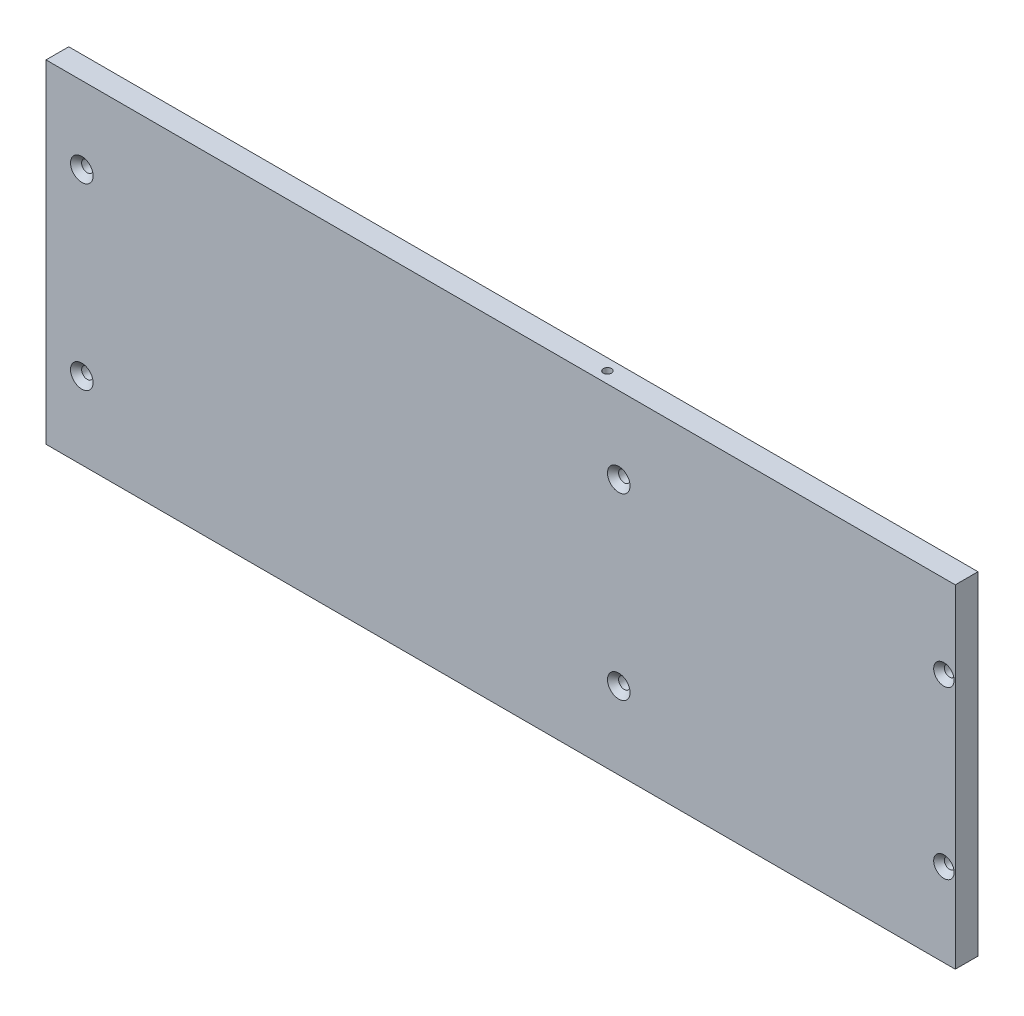
SolidWorks part; units mm, degrees
material "Perspex (TM) GS Acrylic Cast Sheet"
ref_plane "Front Plane" through (0, 0, 0) normal (0, 0, 1) x (1, 0, 0)
ref_plane "Top Plane" through (0, 0, 0) normal (0, 1, 0) x (1, 0, 0)
ref_plane "Right Plane" through (0, 0, 0) normal (1, 0, 0) x (0, 0, -1)
other "Configuration Table"
sketch "Sketch1" plane through (0, 0, 0) normal (0, 0, 1) x (1, 0, 0)
  line L1 (-127, 46.5) -> (127, 46.5)
  line L2 (-127, 46.5) -> (-127, -46.5)
  line L3 (-127, -46.5) -> (127, -46.5)
  line L4 (127, 46.5) -> (127, -46.5)
  line L5 (-127, 46.5) -> (127, -46.5) construction
  line L6 (-127, -46.5) -> (127, 46.5) construction
  point P0 (0, 0)
  dimension "D1" = 93
  dimension "D2" = 254
extrude "Boss-Extrude1" add sketch "Sketch1" along normal blind 6.35
sketch "PSU Holes" plane through (0, 0, 6.35) normal (0, 0, 1) x (1, 0, 0)
  line L0 (-127, 46.5) -> (-127, -46.5) construction
  line L1 (-117, 25) -> (33, 25)
  line L2 (-117, 25) -> (-117, -25)
  line L3 (-117, -25) -> (33, -25)
  line L4 (33, 25) -> (33, -25)
  line L5 (-117, 25) -> (33, -25) construction
  line L6 (-117, -25) -> (33, 25) construction
  point P0 (-42, 0)
  point P5 (-127, 0)
  dimension "D1" = 50
  dimension "D2" = 150
  dimension "D3" = 85
sketch "Front Holes" plane through (0, 0, 0) normal (0, 0, 1) x (1, 0, 0)
  point P0 (123.825, 23.25)
  point P3 (123.825, -23.25)
sketch "Sketch9" plane through (0, 0, 6.35) normal (0, 0, 1) x (1, 0, 0)
  point P0 (123.825, 23.25)
  point P6 (123.825, -23.25)
hole_wizard "CSK for #4 Flat Head Machine Screw1" positions "Sketch9" profile "Sketch10" countersink size "#4" standard "ANSI Inch" end condition through all
sketch "Sketch10" plane through (123.825, 23.25, 6.35) normal (1, 0, 0) x (0, -1, 0)
  line L0 (0, 0) -> (0, 6.35)
  line L1 (0, 6.35) -> (1.4732, 6.35)
  line L2 (1.4732, 6.35) -> (1.4732, 1.5925)
  line L3 (1.4732, 1.5925) -> (2.8575, 0)
  line L5 (2.8575, 0) -> (0, 0)
  line L6 (-1.4732, 1.5925) -> (-2.8575, 0) construction
  line L11 (0, -6.35) -> (0, 107.95) construction
  dimension "Thru Hole Dia." = 2.9464
  dimension "Thru Hole Depth" = 6.35
  dimension "Near C'Sink Dia." = 5.715
  dimension "Near C'Sink Angle" = 82
sketch "Sketch11" plane through (0, 0, 6.35) normal (0, 0, 1) x (1, 0, 0)
  point P0 (-117, 25)
  point P3 (-117, -25)
  point P6 (33, -25)
  point P9 (33, 25)
hole_wizard "CSK for M3 Flat Head Machine Screw1" positions "Sketch11" profile "Sketch12" countersink size "M3" standard "ANSI Metric" end condition through all
sketch "Sketch12" plane through (-117, 25, 6.35) normal (1, 0, 0) x (0, -1, 0)
  line L0 (0, 0) -> (0, 6.35)
  line L1 (0, 6.35) -> (1.6, 6.35)
  line L2 (1.6, 6.35) -> (1.6, 1.55)
  line L3 (1.6, 1.55) -> (3.15, 0)
  line L5 (3.15, 0) -> (0, 0)
  line L6 (-1.6, 1.55) -> (-3.15, 0) construction
  line L11 (0, -6.35) -> (0, 107.95) construction
  dimension "Thru Hole Dia." = 3.2
  dimension "Thru Hole Depth" = 6.35
  dimension "Near C'Sink Dia." = 6.3
  dimension "Near C'Sink Angle" = 90
hole_wizard "CSK for #4 Flat Head Machine Screw2" positions "Sketch13" profile "Sketch14" countersink size "#4" standard "ANSI Inch"
sketch "Sketch13" plane through (0, 0, 0) normal (0, 0, -1) x (-1, 0, 0)
  point P0 (-123.825, 23.25)
  point P6 (-123.825, -23.25)
sketch "Sketch14" plane through (123.825, 23.25, 0) normal (1, 0, 0) x (0, 1, 0)
  line L0 (0, 0) -> (0, 6.35)
  line L1 (0, 6.35) -> (1.4732, 6.35)
  line L2 (1.4732, 6.35) -> (1.4732, 1.5925)
  line L3 (1.4732, 1.5925) -> (2.8575, 0)
  line L5 (2.8575, 0) -> (0, 0)
  line L6 (-1.4732, 1.5925) -> (-2.8575, 0) construction
  line L11 (0, -6.35) -> (0, 107.95) construction
  dimension "Thru Hole Dia." = 2.9464
  dimension "Thru Hole Depth" = 6.35
  dimension "Near C'Sink Dia." = 5.715
  dimension "Near C'Sink Angle" = 82
sketch "Sketch15" plane through (0, 0, 0) normal (0, 0, -1) x (-1, 0, 0)
  point P0 (-33, 25)
  point P3 (-33, -25)
  point P6 (117, -25)
  point P9 (117, 25)
hole_wizard "CSK for M3 Flat Head Machine Screw2" positions "Sketch15" profile "Sketch16" countersink size "M3" standard "ANSI Metric"
sketch "Sketch16" plane through (33, 25, 0) normal (1, 0, 0) x (0, 1, 0)
  line L0 (0, 0) -> (0, 6.35)
  line L1 (0, 6.35) -> (1.6, 6.35)
  line L2 (1.6, 6.35) -> (1.6, 1.55)
  line L3 (1.6, 1.55) -> (3.15, 0)
  line L5 (3.15, 0) -> (0, 0)
  line L6 (-1.6, 1.55) -> (-3.15, 0) construction
  line L11 (0, -6.35) -> (0, 107.95) construction
  dimension "Thru Hole Dia." = 3.2
  dimension "Thru Hole Depth" = 6.35
  dimension "Near C'Sink Dia." = 6.3
  dimension "Near C'Sink Angle" = 90
sketch "Sketch17" plane through (0, 0, 0) normal (0, 1, 0) x (1, 0, 0)
  line L0 (-127, -3.175) -> (127, -3.175) construction
  line L1 (-127, -6.35) -> (-127, 0) construction
  line L2 (127, -6.35) -> (127, 0) construction
  point P6 (26.65, -3.175)
  point P7 (33, -3.175)
  dimension "D1" = 6.35
sketch "Sketch18" plane through (0, 46.5, 0) normal (0, 1, 0) x (1, 0, 0)
  point P0 (26.65, -3.175)
hole_wizard "#4-40 Tapped Hole1" positions "Sketch18" profile "Sketch19" tap size "#4-40" standard "ANSI Inch"
sketch "Sketch19" plane through (26.65, 46.5, 3.175) normal (1, 0, 0) x (0, 0, 1)
  line L0 (0, 0) -> (0, 8.9342)
  line L1 (0, 8.9342) -> (1.1303, 8.255)
  line L2 (1.1303, 8.255) -> (1.1303, 0)
  line L5 (1.1303, 0) -> (0, 0)
  line L10 (0, 8.9342) -> (-1.1303, 8.255) construction
  line L11 (0, -6.35) -> (0, 107.95) construction
  dimension "Tap Drill Dia." = 2.2606
  dimension "Tap Drill Depth" = 8.255
  dimension "Drill Angle" = 118
cosmetic thread "Hole Thread1" parameters "D1"=6.35, "D2"=2.8448
